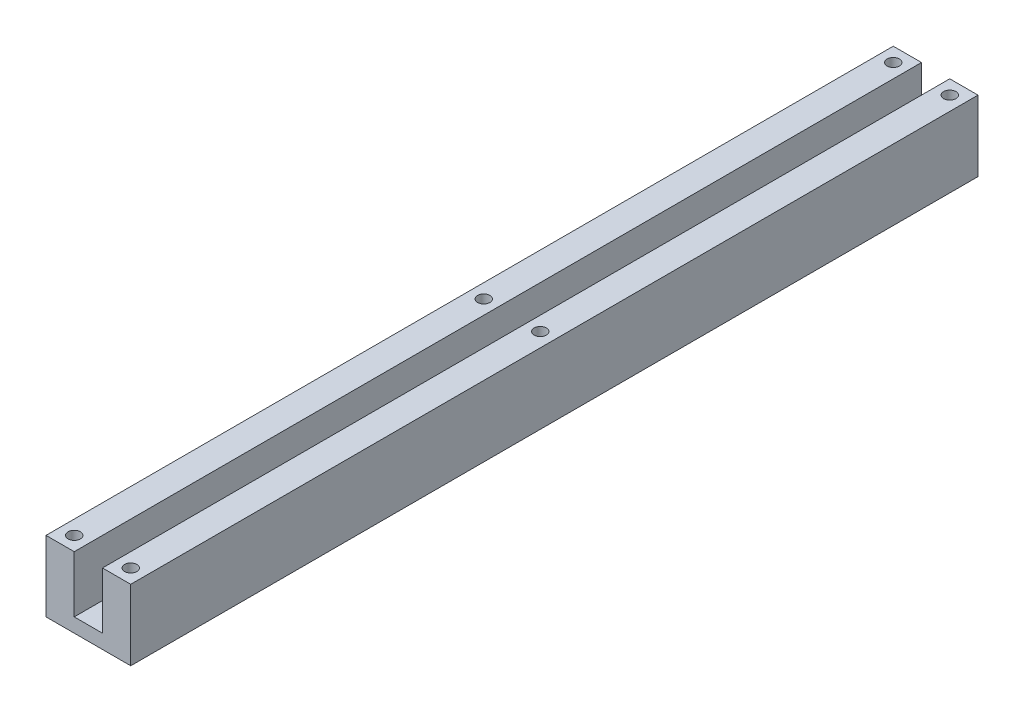
SolidWorks part; units mm, degrees
material "PC High Viscosity"
ref_plane "Front Plane" through (0, 0, 0) normal (0, 0, 1) x (1, 0, 0)
ref_plane "Top Plane" through (0, 0, 0) normal (0, 1, 0) x (1, 0, 0)
ref_plane "Right Plane" through (0, 0, 0) normal (1, 0, 0) x (0, 0, -1)
sketch "Sketch1" plane through (0, 0, 0) normal (0, 0, 1) x (1, 0, 0)
  line L0 (-9.525, 12.7) -> (-3.175, 12.7)
  line L1 (-3.175, 12.7) -> (-3.175, 0)
  line L2 (-3.175, 0) -> (3.175, 0)
  line L3 (3.175, 0) -> (3.175, 12.7)
  line L4 (3.175, 12.7) -> (9.525, 12.7)
  line L5 (-9.525, 12.7) -> (-9.525, -3.175)
  line L6 (-9.525, -3.175) -> (9.525, -3.175)
  line L7 (9.525, -3.175) -> (9.525, 12.7)
  line L8 (0, 0) -> (0, -3.175) construction
  point P2 (0, 0)
  dimension "D1" = 15.875
  dimension "D2" = 6.35
  dimension "D3" = 19.05
  dimension "D4" = 3.175
extrude "Boss-Extrude1" add sketch "Sketch1" along normal mid plane 203.2
sketch "Sketch2" plane through (0, 0, -101.6) normal (0, 0, 1) x (1, 0, 0)
  line L0 (-3.175, 12.7) -> (-9.525, 12.7) construction
  line L1 (-9.525, 12.7) -> (9.525, 12.7)
  line L2 (-9.525, 12.7) -> (-9.525, -3.175)
  line L3 (-9.525, -3.175) -> (9.525, -3.175)
  line L4 (9.525, 12.7) -> (9.525, -3.175)
  line L5 (0, 5.6775) -> (0, -5.9379) construction
  line L7 (-9.525, -3.175) -> (9.525, -3.175) construction
  dimension "D1" = 19.05
extrude "Cut-Extrude1" cut sketch "Sketch2" along normal blind 6.35
sketch "Sketch3" plane through (0, 0, -95.25) normal (0, 0, -1) x (-1, 0, 0)
  line L0 (-9.525, 12.7) -> (-3.175, 12.7) construction
  line L1 (-9.525, 12.7) -> (9.525, 12.7)
  line L2 (-9.525, 12.7) -> (-9.525, -3.175)
  line L3 (-9.525, -3.175) -> (9.525, -3.175)
  line L4 (9.525, 12.7) -> (9.525, -3.175)
  line L5 (9.525, -3.175) -> (-9.525, -3.175) construction
  line L6 (-3.175, 0) -> (3.175, 0) construction
  point P8 (0, -3.175)
  point P11 (0, 0)
  dimension "D1" = 19.05
extrude "Cut-Extrude2" cut sketch "Sketch3" against normal blind 6.35
sketch "Sketch4" plane through (0, 12.7, 0) normal (0, 1, 0) x (1, 0, 0)
  line L0 (9.525, -101.6) -> (9.525, 88.9) construction
  line L1 (-9.525, 88.9) -> (-3.175, 88.9) construction
  line L2 (3.175, 88.9) -> (9.525, 88.9) construction
  line L3 (9.525, -101.6) -> (3.175, -101.6) construction
  line L4 (-6.35, -6.35) -> (6.35, -6.35) construction
  circle A0 centre (6.35, 85.725) radius 1.3891
  circle A1 centre (-6.35, 85.725) radius 1.3891
  circle A2 centre (6.35, -6.35) radius 1.3891
  circle A3 centre (-6.35, -6.35) radius 1.3891
  circle A4 centre (6.35, -98.425) radius 1.3891
  circle A5 centre (-6.35, -98.425) radius 1.3891
  point P16 (9.525, -6.35)
  point P21 (-6.35, 88.9)
  point P26 (6.35, 88.9)
  dimension "D2" = 2.7781
  dimension "D1" = 3.175
extrude "Cut-Extrude3" cut sketch "Sketch4" against normal through all both and the other way through all
